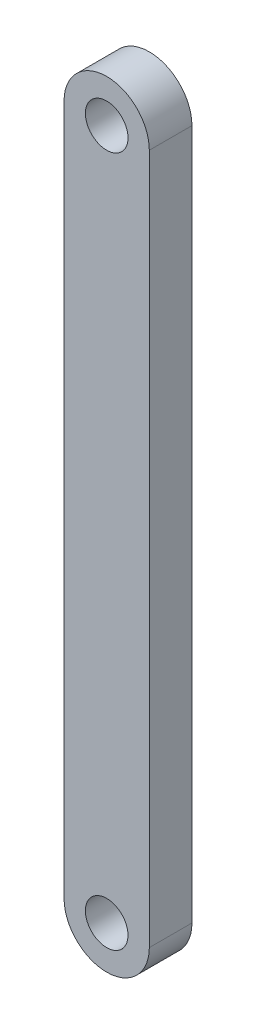
SolidWorks part; units mm, degrees
ref_plane "Front Plane" through (0, 0, 0) normal (0, 0, 1) x (1, 0, 0)
ref_plane "Top Plane" through (0, 0, 0) normal (0, 1, 0) x (1, 0, 0)
ref_plane "Right Plane" through (0, 0, 0) normal (1, 0, 0) x (0, 0, -1)
sketch "Sketch1" plane through (0, 0, 0) normal (0, 0, 1) x (1, 0, 0)
  line L0 (0, 0) -> (0, 102.87) construction
  line L1 (-6.35, 102.87) -> (-6.35, 0)
  line L2 (6.35, 102.87) -> (6.35, 0)
  arc A0 (-6.35, 0) -> (6.35, 0) centre (0, 0) ccw
  arc A1 (6.35, 102.87) -> (-6.35, 102.87) centre (0, 102.87) ccw
  circle A2 centre (0, 102.87) radius 3.175
  circle A3 centre (0, 0) radius 3.175
  dimension "D2" = 12.7
  dimension "D3" = 12.7
  dimension "D4" = 6.35
  dimension "D5" = 6.35
  dimension "D1" = 102.87
extrude "Boss-Extrude1" add sketch "Sketch1" along normal blind 6.35
